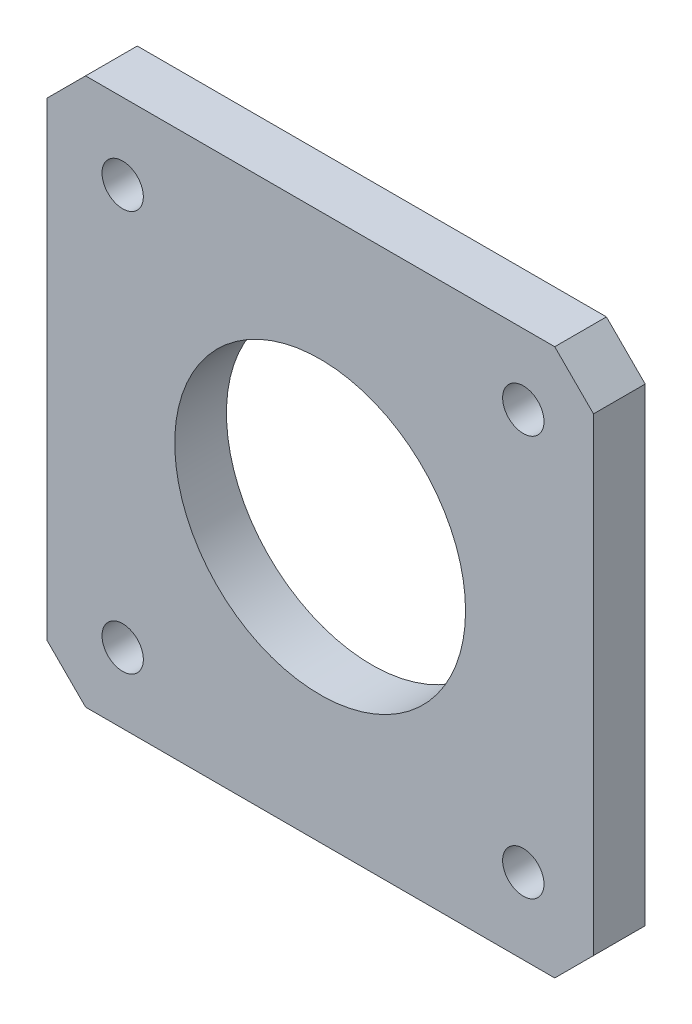
SolidWorks part; units mm, degrees
ref_plane "Front Plane" through (0, 0, 0) normal (0, 0, 1) x (1, 0, 0)
ref_plane "Top Plane" through (0, 0, 0) normal (0, 1, 0) x (1, 0, 0)
ref_plane "Right Plane" through (0, 0, 0) normal (1, 0, 0) x (0, 0, -1)
sketch "Sketch1" plane through (0, 0, 0) normal (0, 0, 1) x (1, 0, 0)
  line L1 (-21.15, -21.15) -> (21.15, -21.15)
  line L2 (-21.15, -21.15) -> (-21.15, 21.15)
  line L3 (-21.15, 21.15) -> (21.15, 21.15)
  line L4 (21.15, -21.15) -> (21.15, 21.15)
  line L5 (-21.15, -21.15) -> (21.15, 21.15) construction
  line L6 (-21.15, 21.15) -> (21.15, -21.15) construction
  circle A0 centre (0, 0) radius 11.25
  circle A1 centre (15.7177, 15.7177) radius 1.6
  circle A2 centre (-15.2792, 15.2792) radius 1.6
  circle A3 centre (-15.2792, -15.7208) radius 1.6
  circle A4 centre (15.7177, -15.2823) radius 1.6
  dimension "D1" = 42.3
  dimension "D3" = 22.5
  dimension "D4" = 31
  dimension "D2" = 42.3
  dimension "D5" = 2
extrude "Boss-Extrude1" add sketch "Sketch1" along normal blind 4
chamfer "Chamfer1" distance 3 angle 45 4 edges at (-21.15, -21.15, 2) (21.15, -21.15, 2) (-21.15, 21.15, 2) (21.15, 21.15, 2)
